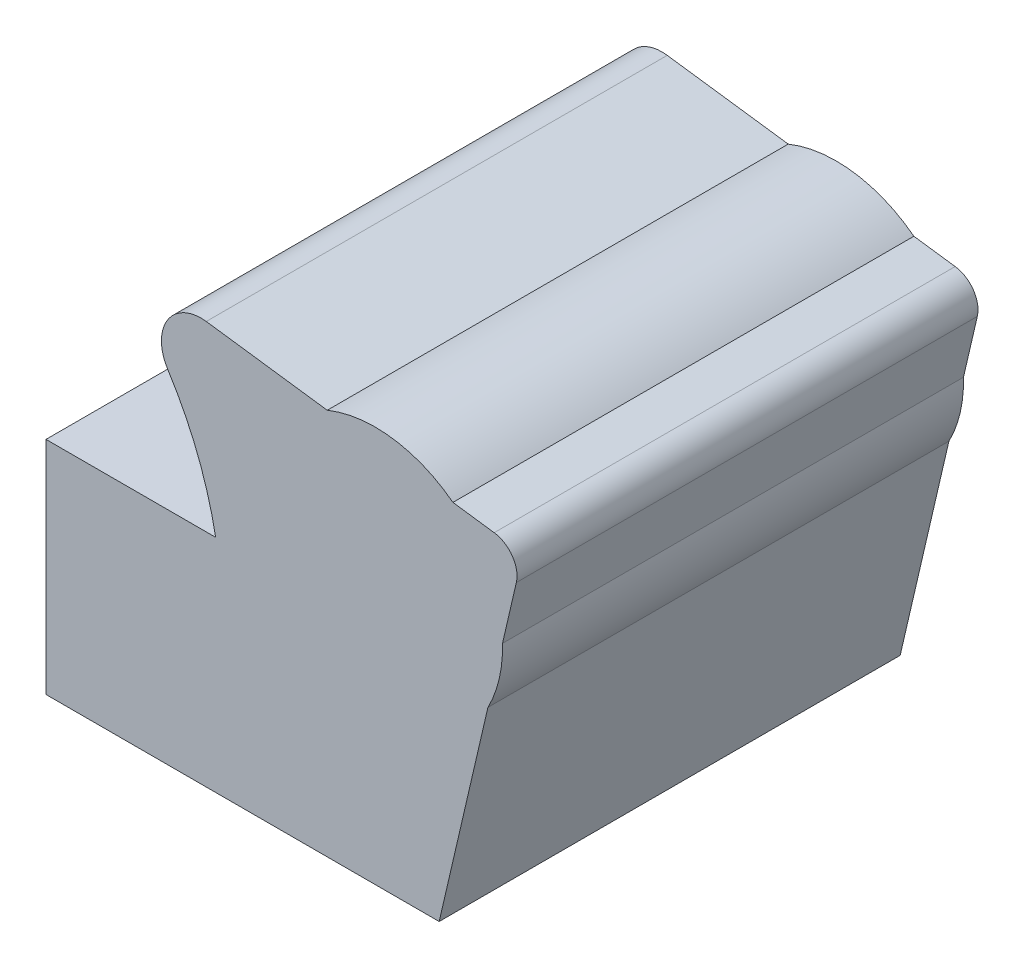
SolidWorks part; units mm, degrees
ref_plane "前视基准面" through (0, 0, 0) normal (0, 0, 1) x (1, 0, 0)
ref_plane "上视基准面" through (0, 0, 0) normal (0, 1, 0) x (1, 0, 0)
ref_plane "右视基准面" through (0, 0, 0) normal (1, 0, 0) x (0, 0, -1)
sketch "草图1" plane through (0, 0, 0) normal (0, 0, 1) x (1, 0, 0)
  line L1 (0, 29.5569) -> (33.8411, 29.5569)
  line L2 (116.7701, 26.4939) -> (125.1562, 47.9624)
  line L3 (152.6325, 126.9813) -> (90.1698, 135.4275)
  line L6 (89.0201, 126.9249) -> (126.841, 106.3205)
  line L8 (0, 0) -> (0, 29.5569)
  line L9 (33.8411, 29.5569) -> (55.4044, 43.1338)
  line L11 (144.001, 0) -> (133.5423, 26.4939)
  line L14 (89.661, -18.3061) -> (89.661, 35.0616) construction
  line L17 (125.1562, 47.9624) -> (140.6985, 47.9624)
  line L18 (140.6985, 47.9624) -> (157.4376, 120.0186)
  line L20 (133.5423, 26.4939) -> (116.7701, 26.4939)
  line L21 (55.4044, 43.1338) -> (55.4044, 95.8971)
  line L22 (0, 0) -> (144.001, 0)
  line L23 (55.4044, 95.8971) -> (92.2029, 95.8971)
  arc A2 (81.7861, 122.3112) -> (92.2029, 95.8971) centre (19.0918, 82.3258) cw
  arc A9 (90.1698, 135.4275) -> (81.7861, 122.3112) centre (89.0201, 126.9249) ccw
  arc A10 (157.4376, 120.0186) -> (152.6325, 126.9813) centre (151.866, 121.3129) ccw
  circle A15 centre (126.841, 106.3205) radius 27.6011
  dimension "D2" = 55.2022
  dimension "D3" = 74.36
  dimension "D4" = 8.58
  dimension "D5" = 5.72
  dimension "D1" = 106.3205
  dimension "D6" = 19.0918
  dimension "D7" = 33.8411
  dimension "D8" = 55.4044
  dimension "D9" = 81.7861
  dimension "D10" = 90.1698
  dimension "D11" = 89.661
  dimension "D12" = 151.866
  dimension "D13" = 92.2029
  dimension "D14" = 116.7701
  dimension "D15" = 125.1562
  dimension "D16" = 126.841
  dimension "D17" = 133.5423
  dimension "D18" = 140.6985
  dimension "D19" = 144.001
  dimension "D20" = 26.4939
  dimension "D21" = 29.5569
  dimension "D22" = 157.4376
  dimension "D23" = 43.1338
  dimension "D24" = 47.9624
extrude "凸台-拉伸1" add sketch "草图1" along normal mid plane 100
sketch "草图2" plane through (0, 0, 50) normal (0, 0, 1) x (1, 0, 0)
  line L0 (125.1562, 47.9624) -> (37.9215, 47.9624)
split "分割1" trim tools "草图2" bodies to split 106 resulting bodies 107 108
delete or keep bodies "实体-删除/保留 1" type keep bodies bodies 107
